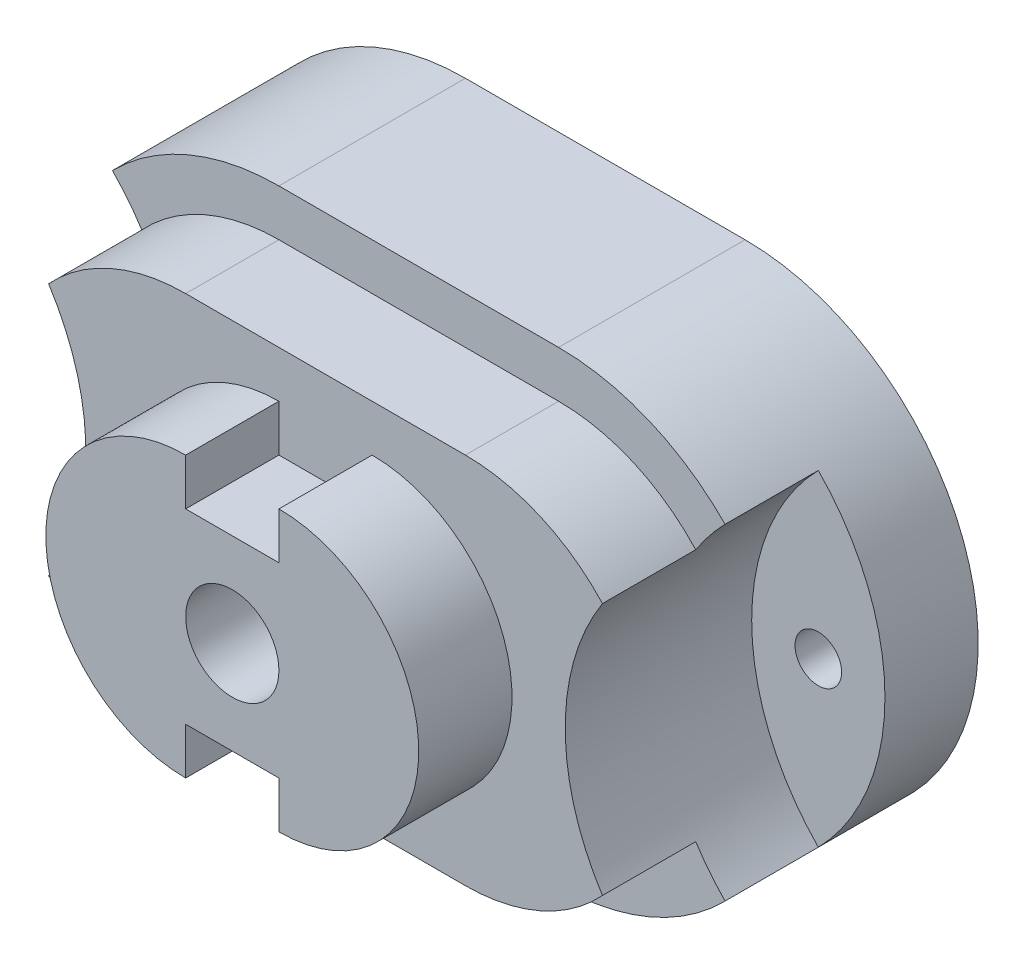
SolidWorks part; units mm, degrees
ref_plane "Front Plane" through (0, 0, 0) normal (0, 0, 1) x (1, 0, 0)
ref_plane "Top Plane" through (0, 0, 0) normal (0, 1, 0) x (1, 0, 0)
ref_plane "Right Plane" through (0, 0, 0) normal (1, 0, 0) x (0, 0, -1)
sketch "Sketch1" plane through (0, 0, 0) normal (0, 0, 1) x (1, 0, 0)
  line L0 (-30, 25) -> (0, 25) construction
  line L1 (-30, 50) -> (0, 50)
  line L2 (-30, 0) -> (0, 0)
  arc A0 (-30, 50) -> (-30, 0) centre (-30, 25) ccw
  arc A1 (0, 0) -> (0, 50) centre (0, 25) ccw
  point P2 (-15, 25)
  dimension "D2" = 25
  dimension "D1" = 30
extrude "Boss-Extrude1" add sketch "Sketch1" along normal blind 20
sketch "Sketch2" plane through (0, 0, 20) normal (0, 0, 1) x (1, 0, 0)
  line L0 (-47.8536, 7.5) -> (-47.8536, 42.5)
  line L1 (17.8536, 7.5) -> (17.8536, 42.5)
  line L2 (17.8536, 42.5) -> (17.8536, 7.5)
  arc A0 (17.8536, 42.5) -> (17.8536, 7.5) centre (35.7071, 25) ccw
  arc A1 (0, 0) -> (0, 50) centre (0, 25) ccw construction
  arc A2 (17.8536, 7.5) -> (17.8536, 42.5) centre (0, 25) ccw
  arc A3 (-47.8536, 42.5) -> (-47.8536, 7.5) centre (-65.7071, 25) cw
  arc A5 (-30, 50) -> (-30, 0) centre (-30, 25) ccw construction
  arc A6 (-47.8536, 42.5) -> (-47.8536, 7.5) centre (-30, 25) ccw
  arc A7 (-47.8536, 42.5) -> (-47.8536, 7.5) centre (-30, 25) ccw
  arc A8 (17.8536, 7.5) -> (17.8536, 42.5) centre (0, 25) ccw
  arc M1 (-30, 50) -> (-30, 0) centre (-30, 25) ccw
  dimension "D1" = 7.5
  dimension "D2" = 7.5
  dimension "D3" = 25
  dimension "D4" = 25
  dimension "D5" = 7.5
  dimension "D6" = 25
extrude "Cut-Extrude10" cut sketch "Sketch2" against normal blind 10 contours L0 M1
sketch "Sketch9" plane through (0, 0, 20) normal (0, 0, 1) x (1, 0, 0)
  line L0 (17.8536, 42.5) -> (17.8536, 7.5)
  arc A0 (17.8536, 42.5) -> (17.8536, 7.5) centre (0, 25) cw
  arc A1 (0, 0) -> (0, 50) centre (0, 25) ccw construction
  dimension "D1" = 25
extrude "Cut-Extrude11" cut sketch "Sketch9" against normal blind 10
sketch "Sketch10" plane through (0, 0, 20) normal (0, 0, 1) x (1, 0, 0)
  line L0 (-30, 25) -> (0, 25) construction
  line L1 (-30, 45) -> (0, 45)
  line L2 (-30, 5) -> (0, 5)
  line L3 (0, 50) -> (-30, 50) construction
  line L4 (-30, 0) -> (0, 0) construction
  arc A0 (-30, 45) -> (-30, 5) centre (-30, 25) ccw
  arc A1 (0, 5) -> (0, 45) centre (0, 25) ccw
  point P2 (-15, 25)
  dimension "D1" = 5
  dimension "D2" = 5
extrude "Boss-Extrude4" add sketch "Sketch10" along normal blind 10
sketch "Sketch11" plane through (0, 0, 30) normal (0, 0, 1) x (1, 0, 0)
  arc A0 (-47.8536, 42.5) -> (-47.8536, 7.5) centre (-65.7071, 25) cw
  arc A1 (-47.8536, 42.5) -> (-47.8536, 7.5) centre (-30, 25) ccw construction
  arc A2 (-47.8536, 42.5) -> (-47.8536, 7.5) centre (-30, 25) ccw
  arc A3 (17.8536, 42.5) -> (17.8536, 7.5) centre (35.7071, 25) ccw
  arc A6 (17.8536, 7.5) -> (17.8536, 42.5) centre (0, 25) ccw construction
  arc A7 (17.8536, 42.5) -> (17.8536, 7.5) centre (0, 25) cw
  dimension "D1" = 25
extrude "Cut-Extrude16" cut sketch "Sketch11" against normal blind 20
sketch "Sketch14" plane through (0, 0, 30) normal (0, 0, 1) x (1, 0, 0)
  line L0 (-20, 40) -> (-20, 35)
  line L1 (-20, 35) -> (-10, 35)
  line L2 (-10, 35) -> (-10, 40)
  line L3 (0, 45) -> (-30, 45) construction
  line L4 (-20, 10) -> (-20, 15)
  line L5 (-20, 15) -> (-10, 15)
  line L6 (-10, 15) -> (-10, 10)
  line L7 (-30, 5) -> (0, 5) construction
  arc A0 (-10, 10) -> (-10, 40) centre (-10, 25) ccw
  arc A1 (-20, 10) -> (-20, 40) centre (-20, 25) cw
  dimension "D10" = 15
  dimension "D11" = 15
  dimension "D1" = 5
  dimension "D2" = 20
  dimension "D3" = 10
  dimension "D4" = 5
  dimension "D5" = 5
  dimension "D6" = 20
  dimension "D7" = 5
  dimension "D8" = 5
  dimension "D9" = 5
extrude "Boss-Extrude6" add sketch "Sketch14" along normal blind 10
sketch "Sketch15" plane through (0, 0, 10) normal (0, 0, 1) x (1, 0, 0)
  circle A0 centre (17.8536, 25) radius 2.5
  circle A1 centre (-47.8536, 25) radius 2.5
  dimension "D1" = 5
  dimension "D2" = 5
  dimension "D3" = 17.5
  dimension "D4" = 17.5
extrude "Cut-Extrude17" cut sketch "Sketch15" against normal blind 33
sketch "Sketch16" plane through (0, 0, 40) normal (0, 0, 1) x (1, 0, 0)
  line L0 (-10, 35) -> (-20, 35) construction
  circle A0 centre (-15, 25) radius 5
  dimension "D1" = 10
  dimension "D2" = 10
  dimension "D3" = 5
hole_wizard "Ø1.2 (1.2) Diameter Hole2" positions "3DSketch2" profile "Sketch18" hole size "Ø1.2" standard "ISO"
sketch3d "3DSketch2"
  point P0 (-15, 25, 40)
sketch "Sketch18" plane through (-15, 25, 40) normal (1, 0, 0) x (0, -1, 0)
  line L0 (0, 0) -> (0, 22.7148)
  line L1 (0, 22.7148) -> (5, 20)
  line L2 (5, 20) -> (5, 0)
  line L5 (5, 0) -> (0, 0)
  line L10 (0, 22.7148) -> (-5, 20) construction
  line L11 (0, -6.35) -> (0, 107.95) construction
  dimension "Hole Dia." = 10
  dimension "Hole Depth" = 20
  dimension "Drill Angle" = 123
